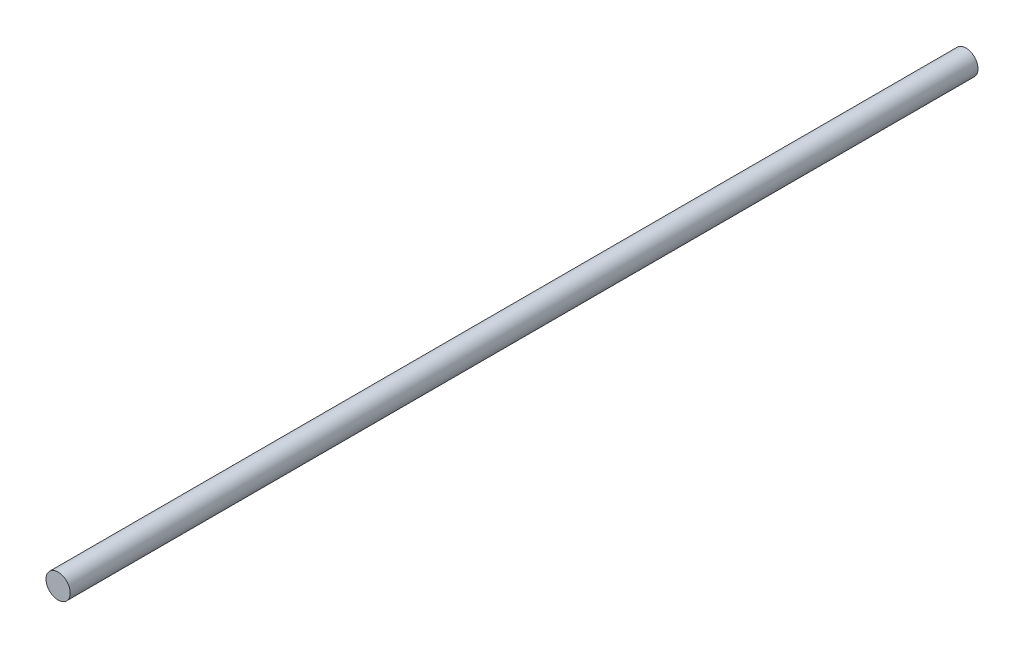
SolidWorks part; units mm, degrees
ref_plane "Front Plane" through (0, 0, 0) normal (0, 0, 1) x (1, 0, 0)
ref_plane "Top Plane" through (0, 0, 0) normal (0, 1, 0) x (1, 0, 0)
ref_plane "Right Plane" through (0, 0, 0) normal (1, 0, 0) x (0, 0, -1)
sketch "Sketch1" plane through (0, 0, 0) normal (0, 0, 1) x (1, 0, 0)
  circle A0 centre (0, 0) radius 8
sketch "Sketch2" plane through (0, 0, 0) normal (0, 0, 1) x (1, 0, 0)
  circle A0 centre (0, 0) radius 4
extrude "Boss-Extrude1" add sketch "Sketch2" along normal blind 300
